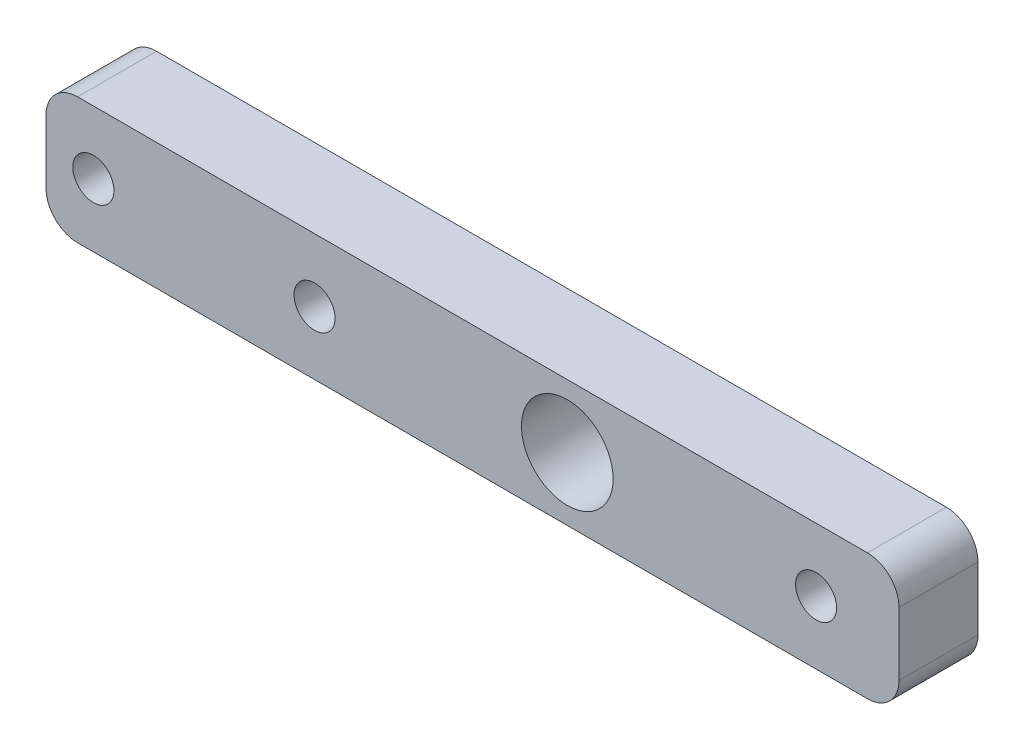
SolidWorks part; units mm, degrees
material "PLA"
ref_plane "Blat stołu" through (0, 0, 0) normal (0, 0, 1) x (1, 0, 0)
ref_plane "Płaszczyzna górna" through (0, 0, 0) normal (0, 1, 0) x (1, 0, 0)
ref_plane "Płaszczyzna prawa" through (0, 0, 0) normal (1, 0, 0) x (0, 0, -1)
sketch "Szkic1" plane through (0, 0, 0) normal (0, 0, 1) x (1, 0, 0)
  line L1 (-25, 4) -> (25, 4)
  line L2 (-27, 2) -> (-27, -2)
  line L3 (-25, -4) -> (25, -4)
  line L4 (27, 2) -> (27, -2)
  line L5 (-27, 4) -> (27, -4) construction
  line L6 (-27, -4) -> (27, 4) construction
  arc A0 (-27, 2) -> (-25, 4) centre (-25, 2) cw
  arc A1 (-27, -2) -> (-25, -4) centre (-25, -2) ccw
  arc A2 (25, 4) -> (27, 2) centre (25, 2) cw
  arc A3 (25, -4) -> (27, -2) centre (25, -2) ccw
  point P0 (0, 0)
  dimension "D3" = 2
  dimension "D4" = 2
  dimension "D5" = 2
  dimension "D6" = 2
  dimension "D1" = 54
  dimension "D2" = 8
extrude "Dodanie-wyciągnięcie1" add sketch "Szkic1" along normal blind 5 contours L1 A2 L4 A3 L3 A1 L2 A0
hole_wizard "Otwór pod śrubę M21" positions "Szkic3" profile "Szkic4" hole size "M2" standard "ISO" end condition up to next
sketch "Szkic3" plane through (0, 0, 5) normal (0, 0, 1) x (1, 0, 0)
  point P0 (-10, 0)
  point P2 (21.75, 0)
  dimension "D1" = 31.75
  dimension "D2" = 10
sketch "Szkic4" plane through (-10, 0, 5) normal (1, 0, 0) x (0, -1, 0)
  line L0 (0, 0) -> (0, 5)
  line L1 (0, 5) -> (1.3, 5)
  line L2 (1.3, 5) -> (1.3, 0)
  line L5 (1.3, 0) -> (0, 0)
  line L11 (0, -6.35) -> (0, 107.95) construction
  dimension "Średnica otworu na wylot" = 2.6
  dimension "Głębokość otworu na wylot" = 5
hole_wizard "Otwór pod śrubę M51" positions "Szkic5" profile "Szkic6" hole size "M5" standard "ISO" end condition up to next
sketch "Szkic5" plane through (0, 0, 5) normal (0, 0, 1) x (1, 0, 0)
  point P0 (6, 0)
  dimension "D1" = 16
sketch "Szkic6" plane through (6, 0, 5) normal (1, 0, 0) x (0, -1, 0)
  line L0 (0, 0) -> (0, 5)
  line L1 (0, 5) -> (2.9, 5)
  line L2 (2.9, 5) -> (2.9, 0)
  line L5 (2.9, 0) -> (0, 0)
  line L11 (0, -6.35) -> (0, 107.95) construction
  dimension "Średnica otworu na wylot" = 5.8
  dimension "Głębokość otworu na wylot" = 5
hole_wizard "Otwór pod śrubę M22" positions "Szkic9" profile "Szkic8" hole size "M2" standard "ISO" end condition up to next
sketch "Szkic9" plane through (0, 0, 5) normal (0, 0, 1) x (1, 0, 0)
  point P0 (-24, 0)
  dimension "D1" = 30
sketch "Szkic8" plane through (-24, 0, 5) normal (1, 0, 0) x (0, -1, 0)
  line L0 (0, 0) -> (0, 5)
  line L1 (0, 5) -> (1.3, 5)
  line L2 (1.3, 5) -> (1.3, 0)
  line L5 (1.3, 0) -> (0, 0)
  line L11 (0, -6.35) -> (0, 107.95) construction
  dimension "Średnica otworu na wylot" = 2.6
  dimension "Głębokość otworu na wylot" = 5
